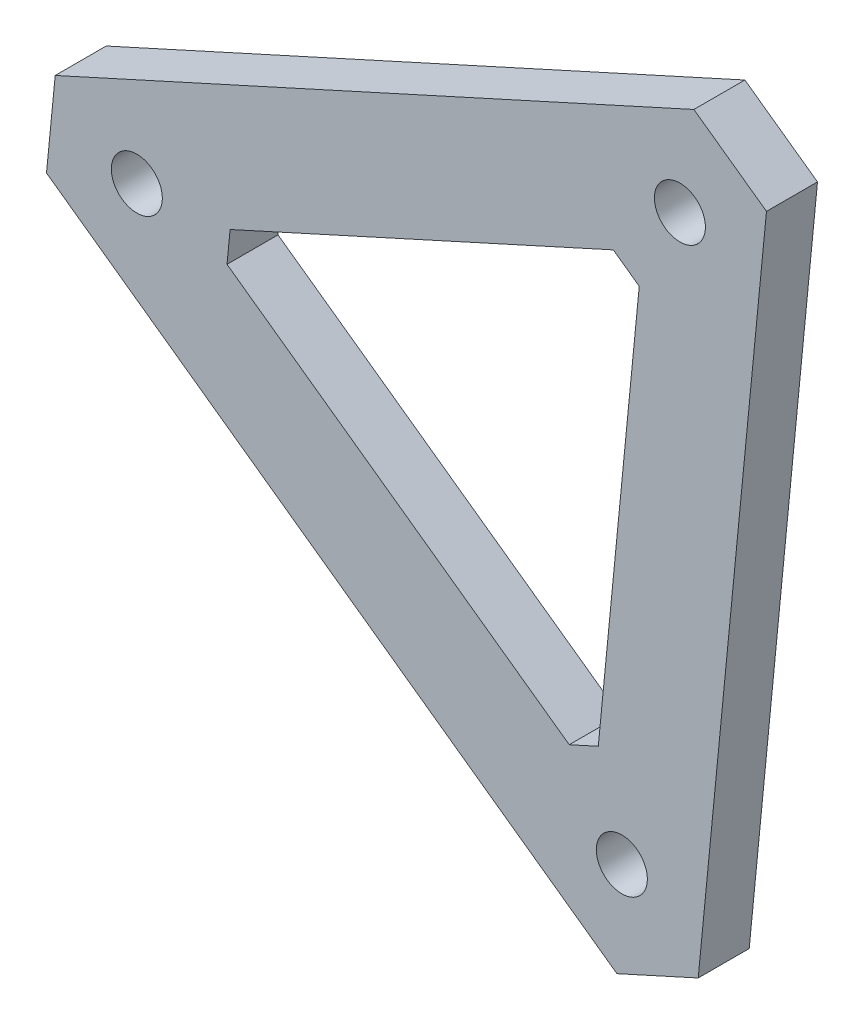
SolidWorks part; units mm, degrees
ref_plane "Front" through (0, 0, 0) normal (0, 0, 1) x (1, 0, 0)
ref_plane "Top" through (0, 0, 0) normal (0, 1, 0) x (1, 0, 0)
ref_plane "Right" through (0, 0, 0) normal (1, 0, 0) x (0, 0, -1)
sketch "Sketch1" plane through (0, 0, 0) normal (0, 0, 1) x (1, 0, 0)
  line L0 (-44.9806, -17.9308) -> (239.0402, -221.1738)
  line L1 (279.516, -202.8023) -> (313.5192, 144.7885)
  line L2 (277.3711, 170.6558) -> (-40.653, 26.308)
  line L3 (44.8927, -12.367) -> (215.3053, -134.3128)
  line L4 (229.7609, -127.7516) -> (250.1628, 80.8029)
  line L5 (237.2528, 90.0412) -> (46.4383, 3.4325)
  line L6 (-42.8168, 4.1886) -> (170.6355, -16.6925) construction
  line L7 (170.6355, -16.6925) -> (295.4451, 157.7221) construction
  line L8 (170.6355, -16.6925) -> (259.2781, -211.9881) construction
  line L9 (250.1628, 80.8029) -> (237.2528, 90.0412)
  line L10 (46.4383, 3.4325) -> (44.8927, -12.367)
  line L11 (215.3053, -134.3128) -> (229.7609, -127.7516)
  line L12 (277.3711, 170.6558) -> (313.5192, 144.7885)
  line L13 (-40.653, 26.308) -> (-44.9806, -17.9308)
  line L14 (239.0402, -221.1738) -> (279.516, -202.8023)
  circle A2 centre (0, 0) radius 12.7
  circle A4 centre (270.4093, 122.736) radius 12.7
  circle A5 centre (241.4971, -172.8134) radius 12.7
  point P3 (31.9827, -3.1287)
  point P4 (228.2153, -143.5512)
  point P5 (251.7084, 96.6025)
  point P9 (222.5331, -131.0322)
  point P10 (243.7078, 85.4221)
  point P11 (45.6655, -4.4672)
  dimension "D3" = 349.25
  dimension "D1" = 44.45
  dimension "D2" = 209.55
  dimension "D7" = 15.875
  dimension "D8" = 15.875
  dimension "D9" = 15.875
extrude "Extrude1" add sketch "Sketch1" against normal blind 25.4
